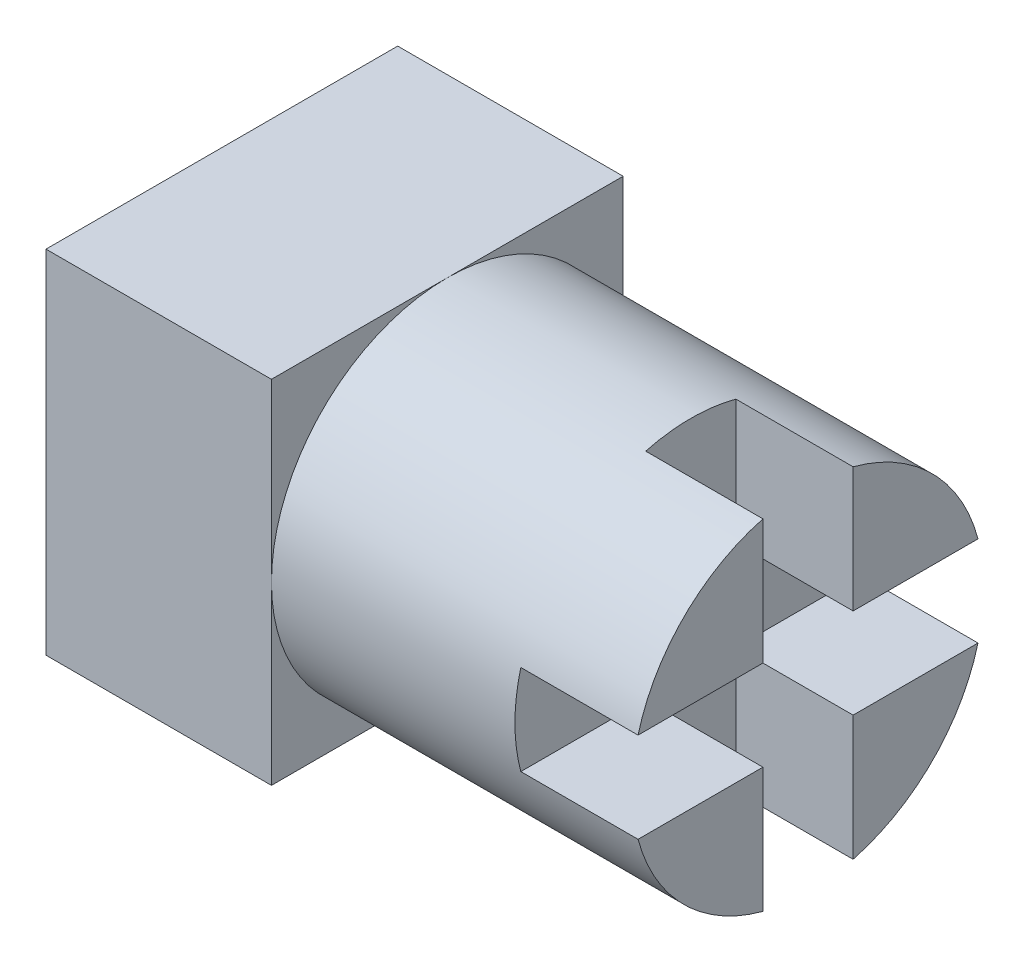
SolidWorks part; units mm, degrees
ref_plane "Front Plane" through (0, 0, 0) normal (0, 0, 1) x (1, 0, 0)
ref_plane "Top Plane" through (0, 0, 0) normal (0, 1, 0) x (1, 0, 0)
ref_plane "Right Plane" through (0, 0, 0) normal (1, 0, 0) x (0, 0, -1)
sketch "Sketch1" plane through (0, 0, 0) normal (1, 0, 0) x (0, 0, -1)
  line L1 (-7.8, 7.8) -> (7.8, 7.8)
  line L2 (-7.8, 7.8) -> (-7.8, -7.8)
  line L3 (-7.8, -7.8) -> (7.8, -7.8)
  line L4 (7.8, 7.8) -> (7.8, -7.8)
  line L5 (-7.8, 7.8) -> (7.8, -7.8) construction
  line L6 (-7.8, -7.8) -> (7.8, 7.8) construction
  point P0 (0, 0)
  dimension "D1" = 15.6
  dimension "D2" = 15.6
extrude "Boss-Extrude1" add sketch "Sketch1" along normal blind 10
sketch "Sketch2" plane through (10, 0, 0) normal (1, 0, 0) x (0, 0, -1)
  circle A0 centre (0, 0) radius 7.8
  dimension "D1" = 15.6
extrude "Boss-Extrude2" add sketch "Sketch2" along normal blind 16
sketch "Sketch3" plane through (26, 0, 0) normal (1, 0, 0) x (0, 0, -1)
  line L12 (0, -7.8) -> (7.8, -7.8) construction
  line L13 (-2, 7.8) -> (2, 7.8)
  line L14 (-2, 7.8) -> (-2, -7.8)
  line L15 (-2, -7.8) -> (2, -7.8)
  line L16 (2, 7.8) -> (2, -7.8)
  line L17 (-2, 7.8) -> (2, -7.8) construction
  line L18 (-2, -7.8) -> (2, 7.8) construction
  line L19 (7.8, 0) -> (7.8, 7.8) construction
  line L20 (-7.8, -2) -> (7.8, -2)
  line L21 (-7.8, -2) -> (-7.8, 2)
  line L22 (-7.8, 2) -> (7.8, 2)
  line L23 (7.8, -2) -> (7.8, 2)
  line L24 (-7.8, -2) -> (7.8, 2) construction
  line L25 (-7.8, 2) -> (7.8, -2) construction
  point P0 (0, 0)
  point P8 (0, 0)
  circle M10 centre (0, 0) radius 7.8
  dimension "D1" = 4
  dimension "D2" = 4
extrude "Cut-Extrude2" cut sketch "Sketch3" against normal blind 5.2 contours L22 L20 L14 M10 | L14 L22 L16 M10 | L22 L16 L20 M10 | L20 L14 L16 M10 | L21 L20 M10 | L22 L21 M10 | L13 L14 M10 | L16 L13 M10 | L23 L22 M10 | L20 L23 M10 | L22 L14 L20 L16
